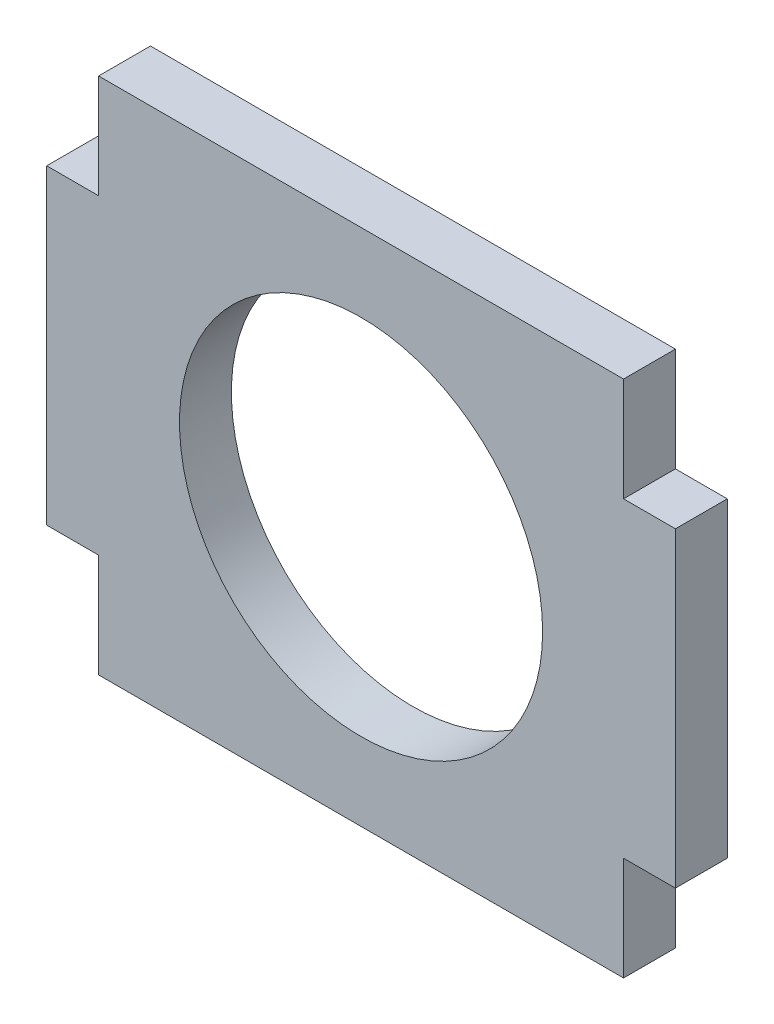
SolidWorks part; units mm, degrees
material "6061-T6 (SS)"
ref_plane "Front Plane" through (0, 0, 0) normal (0, 0, 1) x (1, 0, 0)
ref_plane "Top Plane" through (0, 0, 0) normal (0, 1, 0) x (1, 0, 0)
ref_plane "Right Plane" through (0, 0, 0) normal (1, 0, 0) x (0, 0, -1)
sketch "Sketch1" plane through (0, 0, 0) normal (0, 0, 1) x (1, 0, 0)
  line L0 (-19.2405, -9.525) -> (-19.2405, 9.525)
  line L1 (19.2405, -9.525) -> (19.2405, 9.525)
  line L2 (19.2405, 9.525) -> (16.0655, 9.525)
  line L3 (16.0655, 9.525) -> (16.0655, 15.875)
  line L4 (16.0655, 15.875) -> (-16.0655, 15.875)
  line L5 (-16.0655, 15.875) -> (-16.0655, 9.525)
  line L6 (-16.0655, 9.525) -> (-19.2405, 9.525)
  line L7 (-19.2405, -9.525) -> (-16.0655, -9.525)
  line L8 (-16.0655, -9.525) -> (-16.0655, -15.875)
  line L9 (-16.0655, -15.875) -> (16.0655, -15.875)
  line L10 (16.0655, -15.875) -> (16.0655, -9.525)
  line L11 (16.0655, -9.525) -> (19.2405, -9.525)
  line L12 (0, 0) -> (0, -15.875) construction
  line L13 (0, 0) -> (0, 15.875) construction
  circle A0 centre (0, 0) radius 11.1125
  point P6 (-19.2405, 0)
  point P9 (19.2405, 0)
  dimension "D1" = 22.225
  dimension "D2" = 32.131
  dimension "D3" = 3.175
  dimension "D4" = 6.35
  dimension "D5" = 31.75
extrude "Boss-Extrude1" add sketch "Sketch1" along normal blind 3.175
